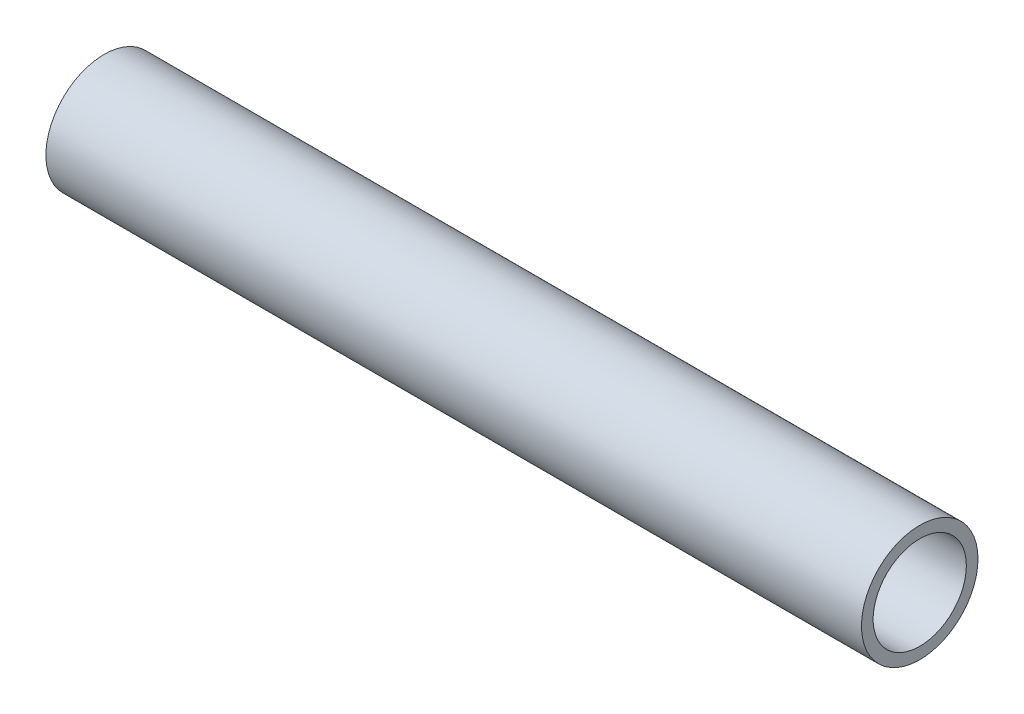
SolidWorks part; units mm, degrees
ref_plane "Plan de face" through (0, 0, 0) normal (0, 0, 1) x (1, 0, 0)
ref_plane "Plan de dessus" through (0, 0, 0) normal (0, 1, 0) x (1, 0, 0)
ref_plane "Plan de droite" through (0, 0, 0) normal (1, 0, 0) x (0, 0, -1)
sketch "Esquisse2" plane through (0, 0, 0) normal (1, 0, 0) x (0, 0, -1)
  circle A0 centre (0, 0) radius 5
  circle A1 centre (0, 0) radius 4
  dimension "D1" = 8
  dimension "D2" = 10
extrude "Boss.-Extru.1" add sketch "Esquisse2" along normal blind 70
